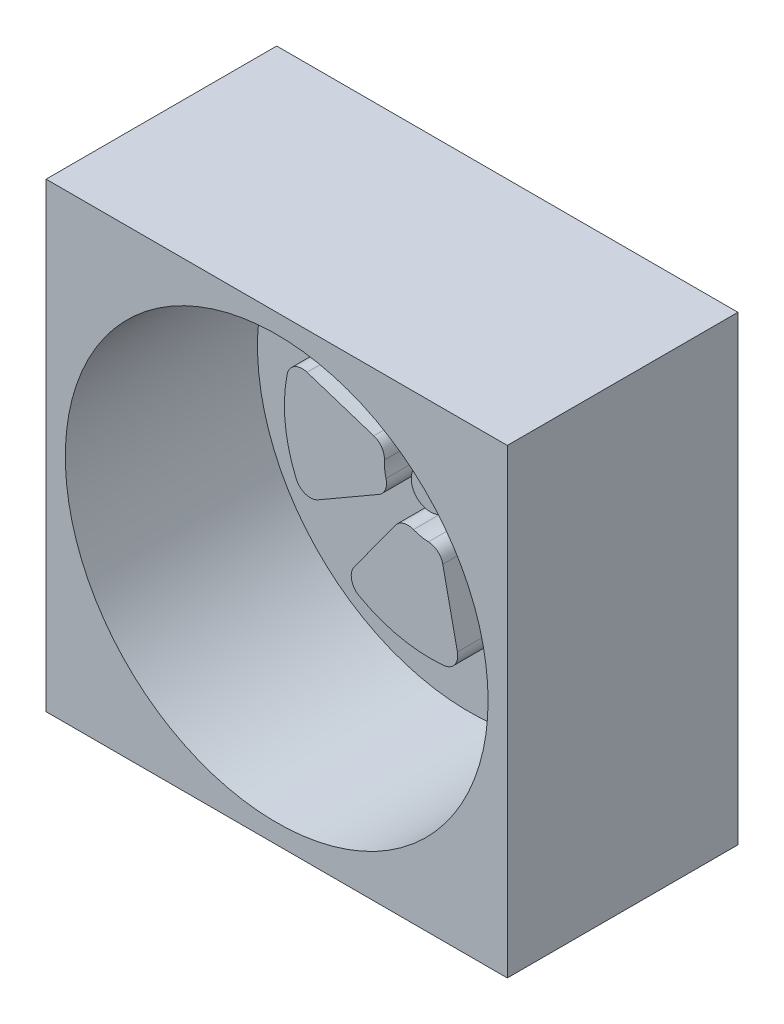
SolidWorks part; units mm, degrees
ref_plane "Alzado" through (0, 0, 0) normal (0, 0, 1) x (1, 0, 0)
ref_plane "Planta" through (0, 0, 0) normal (0, 1, 0) x (1, 0, 0)
ref_plane "Vista lateral" through (0, 0, 0) normal (1, 0, 0) x (0, 0, -1)
sketch "Croquis1" plane through (0, 0, 0) normal (0, 0, 1) x (1, 0, 0)
  circle A0 centre (0, 0) radius 30
  dimension "D1" = 60
extrude "Saliente-Extruir1" add sketch "Croquis1" along normal blind 30
sketch "Croquis2" plane through (0, 0, 30) normal (0, 0, 1) x (1, 0, 0)
  circle A0 centre (0, 0) radius 27.5
  dimension "D1" = 55
extrude "Cortar-Extruir1" cut sketch "Croquis2" against normal blind 25
sketch "Croquis3" plane through (0, 0, 5) normal (0, 0, 1) x (1, 0, 0)
  circle A0 centre (0, 0) radius 2.5
  dimension "D1" = 5
extrude "Saliente-Extruir2" add sketch "Croquis3" along normal blind 5
sketch "Croquis4" plane through (0, 0, 5) normal (0, 0, 1) x (1, 0, 0)
  line L0 (0, 2.5) -> (0, 5.5) construction
  circle A0 centre (0, 0) radius 2.5
  circle A1 centre (0, 0) radius 5.5
  circle A2 centre (0, 0) radius 2.5 construction
  dimension "D1" = 3
extrude "Cortar-Extruir2" cut sketch "Croquis4" against normal blind 2
sketch "Croquis6" plane through (0, 0, 30) normal (0, 0, 1) x (1, 0, 0)
  line L1 (30, -30) -> (-30, -30)
  line L2 (30, -30) -> (30, 30)
  line L3 (30, 30) -> (-30, 30)
  line L4 (-30, -30) -> (-30, 30)
  line L5 (30, -30) -> (-30, 30) construction
  line L6 (30, 30) -> (-30, -30) construction
  circle A0 centre (0, 0) radius 27.5
  circle A1 centre (0, 0) radius 27.5 construction
  circle A2 centre (0, 0) radius 30 construction
  point P0 (0, 0)
extrude "Saliente-Extruir3" add sketch "Croquis6" against normal blind 30
sketch "Croquis7" plane through (0, 0, 5) normal (0, 0, 1) x (1, 0, 0)
  line L0 (0, 6) -> (0, 19)
  line L2 (2.4404, 5.4813) -> (7.728, 17.3574)
  line L6 (5.7063, 1.8541) -> (18.0701, 5.8713)
  line L8 (5.9671, -0.6272) -> (18.8959, -1.986)
  line L12 (3.5267, -4.8541) -> (11.1679, -15.3713)
  line L14 (1.2475, -5.8689) -> (3.9503, -18.5848)
  line L18 (-3.5267, -4.8541) -> (-11.1679, -15.3713)
  line L20 (-5.1962, -3) -> (-16.4545, -9.5)
  line L24 (-5.7063, 1.8541) -> (-18.0701, 5.8713)
  line L26 (-4.4589, 4.0148) -> (-14.1198, 12.7135)
  line L30 (1.2475, 5.8689) -> (3.9503, 18.5848) [skipped]
  line L31 (3.5267, 4.8541) -> (11.1679, 15.3713) [skipped]
  line L32 (4.4589, 4.0148) -> (14.1198, 12.7135) [skipped]
  line L33 (5.1962, 3) -> (16.4545, 9.5) [skipped]
  line L34 (5.9671, 0.6272) -> (18.8959, 1.986) [skipped]
  line L35 (5.7063, -1.8541) -> (18.0701, -5.8713) [skipped]
  line L36 (5.1962, -3) -> (16.4545, -9.5) [skipped]
  line L37 (4.4589, -4.0148) -> (14.1198, -12.7135) [skipped]
  line L38 (2.4404, -5.4813) -> (7.728, -17.3574) [skipped]
  line L39 (0, -6) -> (0, -19) [skipped]
  line L40 (-1.2475, -5.8689) -> (-3.9503, -18.5848) [skipped]
  line L41 (-2.4404, -5.4813) -> (-7.728, -17.3574) [skipped]
  line L42 (-4.4589, -4.0148) -> (-14.1198, -12.7135) [skipped]
  line L43 (-5.7063, -1.8541) -> (-18.0701, -5.8713) [skipped]
  line L44 (-5.9671, -0.6272) -> (-18.8959, -1.986) [skipped]
  line L45 (-5.9671, 0.6272) -> (-18.8959, 1.986) [skipped]
  line L46 (-5.1962, 3) -> (-16.4545, 9.5) [skipped]
  line L47 (-3.5267, 4.8541) -> (-11.1679, 15.3713) [skipped]
  line L48 (-2.4404, 5.4813) -> (-7.728, 17.3574) [skipped]
  line L49 (-1.2475, 5.8689) -> (-3.9503, 18.5848) [skipped]
  arc A0 (-5.7063, 1.8541) -> (-5.1962, -3) centre (0, 0) ccw
  arc A1 (0, 19) -> (-14.1198, 12.7135) centre (0, 0) ccw
  arc A2 (18.0701, 5.8713) -> (7.728, 17.3574) centre (0, 0) ccw
  arc A3 (11.1679, -15.3713) -> (18.8959, -1.986) centre (0, 0) ccw
  arc A4 (-11.1679, -15.3713) -> (3.9503, -18.5848) centre (0, 0) ccw
  arc A5 (-18.0701, 5.8713) -> (-16.4545, -9.5) centre (0, 0) ccw
  arc A6 (0, 6) -> (-4.4589, 4.0148) centre (0, 0) ccw
  arc A7 (5.7063, 1.8541) -> (2.4404, 5.4813) centre (0, 0) ccw
  arc A8 (3.5267, -4.8541) -> (5.9671, -0.6272) centre (0, 0) ccw
  arc A9 (-3.5267, -4.8541) -> (1.2475, -5.8689) centre (0, 0) ccw
  point P66 (0, 0)
  dimension "D1" = 12
  dimension "D2" = 38
  dimension "D3" = 30
extrude "Saliente-Extruir5" add sketch "Croquis7" along normal blind 5
fillet "Redondeo1" radius 2 20 edges at (-18.0701, 5.8713, 7.5) (-14.1198, 12.7135, 7.5) (0, 19, 7.5) (7.728, 17.3574, 7.5) (18.0701, 5.8713, 7.5) (18.8959, -1.986, 7.5) (11.1679, -15.3713, 7.5) (3.9503, -18.5848, 7.5) (-11.1679, -15.3713, 7.5) (-16.4545, -9.5, 7.5) (-4.4589, 4.0148, 7.5) (0, 6, 7.5) (-5.7063, 1.8541, 7.5) (-5.1962, -3, 7.5) (-3.5267, -4.8541, 7.5) (1.2475, -5.8689, 7.5) (3.5267, -4.8541, 7.5) (5.9671, -0.6272, 7.5) (5.7063, 1.8541, 7.5) (2.4404, 5.4813, 7.5)
